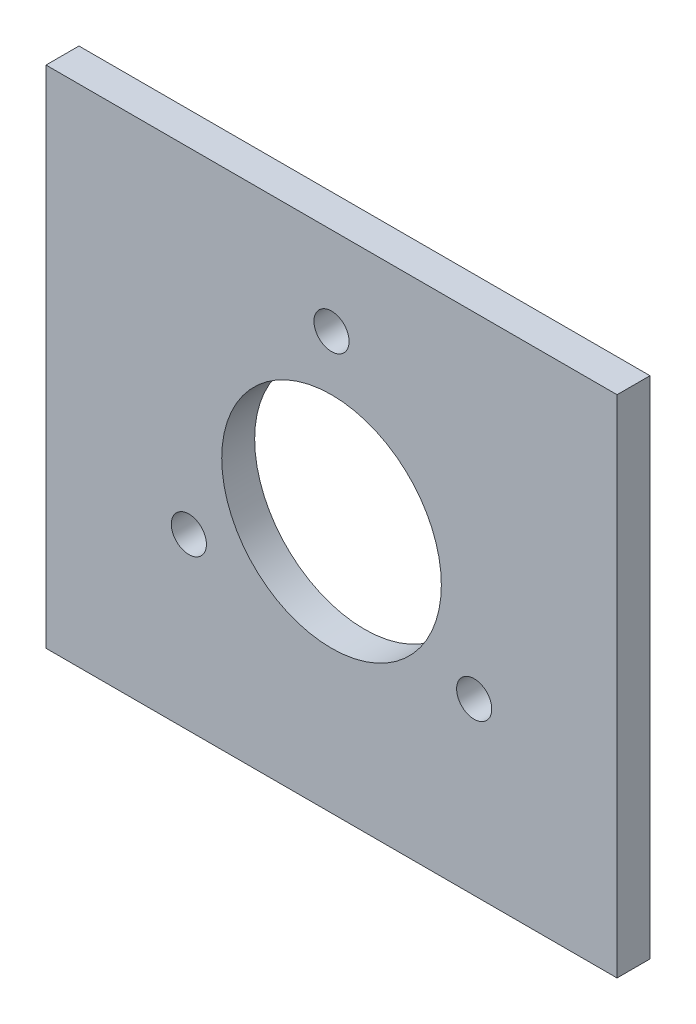
SolidWorks part; units mm, degrees
ref_plane "前视基准面" through (0, 0, 0) normal (0, 0, 1) x (1, 0, 0)
ref_plane "上视基准面" through (0, 0, 0) normal (0, 1, 0) x (1, 0, 0)
ref_plane "右视基准面" through (0, 0, 0) normal (1, 0, 0) x (0, 0, -1)
other "Configuration Table"
sketch "草图1" plane through (0, 0, 0) normal (0, 0, 1) x (1, 0, 0)
  line L1 (26, -23) -> (-26, -23)
  line L2 (26, -23) -> (26, 23)
  line L3 (26, 23) -> (-26, 23)
  line L4 (-26, -23) -> (-26, 23)
  line L5 (26, -23) -> (-26, 23) construction
  line L6 (26, 23) -> (-26, -23) construction
  point P0 (0, 0)
  dimension "D1" = 52
  dimension "D2" = 46
extrude "凸台-拉伸1" add sketch "草图1" along normal blind 3
sketch "草图2" plane through (0, 0, 3) normal (0, 0, 1) x (1, 0, 0)
  line L0 (0, 0) -> (0, 15) construction
  circle A0 centre (0, 0) radius 15 construction
  circle A1 centre (0, 0) radius 15 construction
  circle A2 centre (0, 0) radius 10
  circle A3 centre (0, 15) radius 1.6
  circle A4 centre (12.9904, -7.5) radius 1.6
  circle A5 centre (-12.9904, -7.5) radius 1.6
  point P13 (0, 0)
  dimension "D1" = 30
  dimension "D2" = 20
  dimension "D3" = 3.2
  dimension "D4" = 3
extrude "切除-拉伸1" cut sketch "草图2" against normal through all
